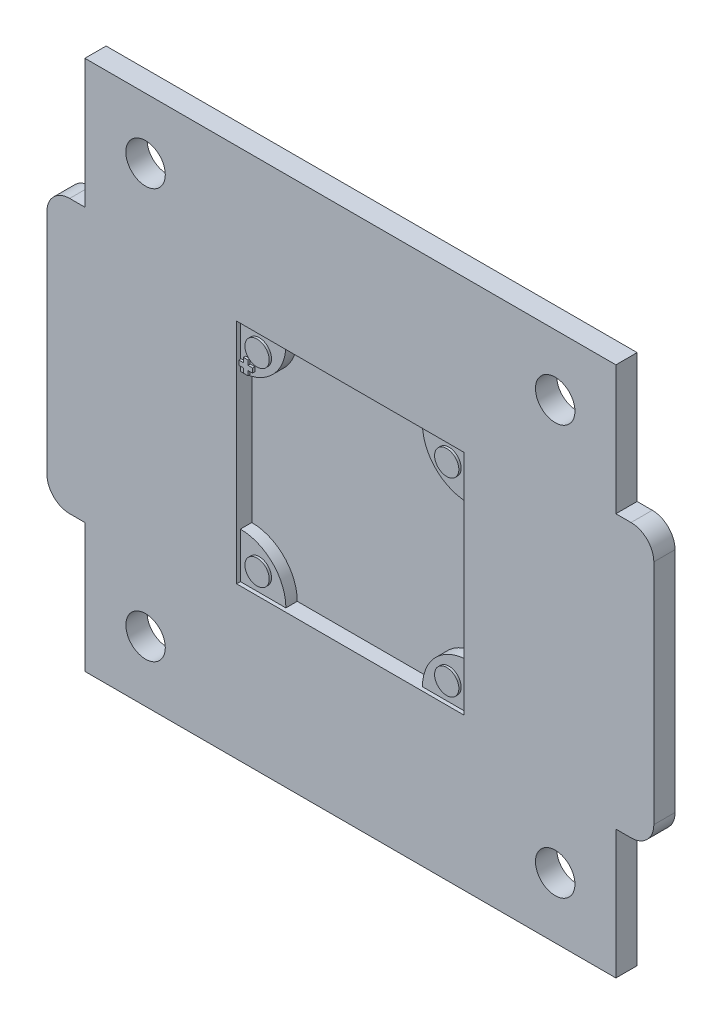
SolidWorks part; units mm, degrees
ref_plane "前视基准面" through (0, 0, 0) normal (0, 0, 1) x (1, 0, 0)
ref_plane "上视基准面" through (0, 0, 0) normal (0, 1, 0) x (1, 0, 0)
ref_plane "右视基准面" through (0, 0, 0) normal (1, 0, 0) x (0, 0, -1)
sketch "草图1" plane through (0, 0, 0) normal (0, 0, 1) x (1, 0, 0)
  line L0 (35, 70) -> (35, 0) construction
  line L1 (0, 0) -> (70, 0)
  line L2 (0, 0) -> (0, 70)
  line L3 (0, 70) -> (70, 70)
  line L4 (70, 0) -> (70, 70)
  line L5 (0, 35) -> (70, 35) construction
  line L6 (70, 17) -> (72, 17)
  line L7 (0, 53) -> (-2, 53)
  line L8 (0, 53) -> (0, 17)
  line L9 (0, 17) -> (-2, 17)
  line L10 (-5, 50) -> (-5, 20)
  line L11 (75, 50) -> (75, 20)
  line L12 (70, 53) -> (72, 53)
  line L13 (70, 53) -> (70, 17)
  arc A0 (-2, 17) -> (-5, 20) centre (-2, 20) cw
  arc A1 (-2, 53) -> (-5, 50) centre (-2, 50) ccw
  arc A2 (72, 17) -> (75, 20) centre (72, 20) ccw
  arc A3 (72, 53) -> (75, 50) centre (72, 50) cw
  point P6 (35, 70)
  point P10 (0, 35)
  point P15 (-5, 35)
  point P18 (-5, 17)
  point P21 (-5, 53)
  dimension "D4" = 3
  dimension "D1" = 70
  dimension "D2" = 5
  dimension "D3" = 36
extrude "凸台-拉伸1" add sketch "草图1" along normal blind 2.8 contours L7 A1 L10 A0 L9 L2 | L1 L4 L3 L2 | A3 L12 L4 L6 A2 L11
sketch "草图2" plane through (0, 0, 2.8) normal (0, 0, 1) x (1, 0, 0)
  line L0 (0, 70) -> (70, 70) construction
  line L1 (35, 70) -> (35, 0) construction
  line L2 (0, 0) -> (70, 0) construction
  line L3 (-5, 50) -> (-5, 20) construction
  line L4 (-5, 35) -> (75, 35) construction
  line L5 (75, 50) -> (75, 20) construction
  line L7 (20, 50) -> (50, 50)
  line L8 (20, 50) -> (20, 20)
  line L9 (20, 20) -> (50, 20)
  line L10 (50, 50) -> (50, 20)
  point P6 (35, 70)
  point P17 (35, 50)
  point P18 (20, 35)
  dimension "D1" = 30
extrude "切除-拉伸1" cut sketch "草图2" against normal blind 2
sketch "草图3" plane through (0, 0, 2.8) normal (0, 0, 1) x (1, 0, 0)
  line L0 (0, 70) -> (0, 0) construction
  line L1 (0, 70) -> (70, 70) construction
  line L2 (0, 53) -> (0, 70) construction
  line L3 (70, 0) -> (70, 70) construction
  line L4 (70, 53) -> (70, 70) construction
  line L5 (0, 35) -> (70, 35) construction
  line L6 (35, 70) -> (35, 0) construction
  line L7 (0, 0) -> (70, 0) construction
  circle A0 centre (8, 62) radius 2.6
  circle A1 centre (62, 62) radius 2.6
  circle A2 centre (8, 8) radius 2.6
  circle A3 centre (62, 8) radius 2.6
  point P18 (35, 70)
  point P19 (0, 35)
  dimension "D3" = 5.2
  dimension "D1" = 8
  dimension "D2" = 8
extrude "切除-拉伸2" cut sketch "草图3" against normal blind 3
sketch "草图4" plane through (0, 0, 0) normal (0, 0, 1) x (1, 0, 0)
  line L0 (20, 35) -> (50, 35) construction
  line L1 (20, 50) -> (50, 50) construction
  line L2 (20, 50) -> (20, 20) construction
  line L3 (20, 20) -> (50, 20) construction
  line L4 (50, 50) -> (50, 20) construction
  line L5 (35, 50) -> (35, 20) construction
  line L6 (20, 44) -> (20, 50)
  line L7 (20, 50) -> (26, 50)
  line L8 (50, 44) -> (50, 50)
  line L9 (50, 50) -> (44, 50)
  line L10 (50, 20) -> (44, 20)
  line L11 (50, 26) -> (50, 20)
  line L12 (20, 26) -> (20, 20)
  line L13 (20, 20) -> (26, 20)
  arc A0 (26, 50) -> (20, 44) centre (20, 50) cw
  arc A1 (44, 50) -> (50, 44) centre (50, 50) ccw
  arc A2 (44, 20) -> (50, 26) centre (50, 20) cw
  arc A3 (26, 20) -> (20, 26) centre (20, 20) ccw
  point P10 (35, 20)
  point P11 (20, 35)
  dimension "D1" = 6
extrude "凸台-拉伸2" add sketch "草图4" along normal blind 2.3
sketch "草图6" plane through (0, 0, 2.3) normal (0, 0, 1) x (1, 0, 0)
  line L0 (20, 35) -> (50, 35) construction
  line L1 (20, 50) -> (50, 50) construction
  line L2 (20, 50) -> (20, 20) construction
  line L3 (20, 20) -> (50, 20) construction
  line L4 (50, 50) -> (50, 20) construction
  line L5 (35, 50) -> (35, 20) construction
  line L6 (20.1, 45.5) -> (20.7, 45.5)
  line L7 (20.7, 45.5) -> (20.7, 46.1)
  line L8 (20.7, 46.1) -> (21.3, 46.1)
  line L9 (21.3, 46.1) -> (21.3, 45.5)
  line L10 (21.3, 45.5) -> (21.9, 45.5)
  line L11 (21.9, 45.5) -> (21.9, 44.9)
  line L12 (21.9, 44.9) -> (21.3, 44.9)
  line L13 (21.3, 44.9) -> (21.3, 44.3)
  line L14 (21.3, 44.3) -> (20.7, 44.3)
  line L15 (20.7, 44.3) -> (20.7, 44.9)
  line L16 (20.7, 44.9) -> (20.1, 44.9)
  line L17 (20.1, 44.9) -> (20.1, 45.5)
  circle A4 centre (22.5, 47.5) radius 1.6
  circle A5 centre (47.5, 47.5) radius 1.6
  circle A6 centre (47.5, 22.5) radius 1.6
  circle A7 centre (22.5, 22.5) radius 1.6
  point P10 (35, 20)
  point P11 (20, 35)
  point P31 (21, 46.1)
  dimension "D1" = 2.5
  dimension "D2" = 2.5
  dimension "D3" = 3.2
  dimension "D4" = 0.6
  dimension "D5" = 0.6
  dimension "D6" = 0.1
  dimension "D7" = 3.9
extrude "凸台-拉伸3" add sketch "草图6" along normal blind 0.3
